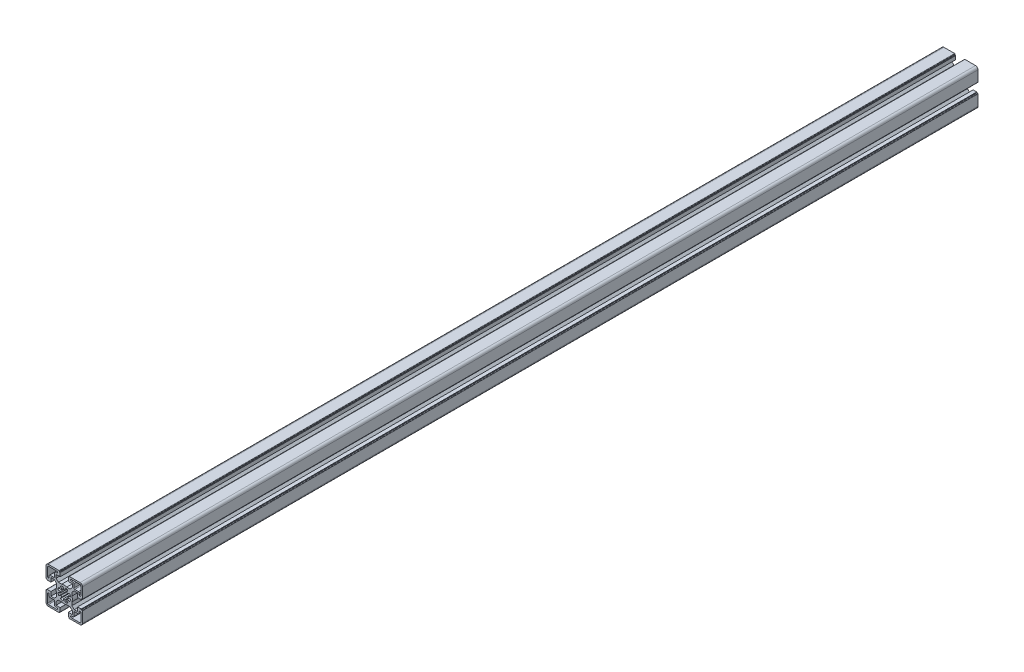
SolidWorks part; units mm, degrees
material "7079 Alloy"
ref_plane "Front Plane" through (0, 0, 0) normal (0, 0, 1) x (1, 0, 0)
ref_plane "Top Plane" through (0, 0, 0) normal (0, 1, 0) x (1, 0, 0)
ref_plane "Right Plane" through (0, 0, 0) normal (1, 0, 0) x (0, 0, -1)
sketch "Sketch1" plane through (0, 0, 0) normal (0, 0, 1) x (1, 0, 0)
  line L0 (0, 34.901) -> (0, -38.8683) construction
  line L1 (-27.7848, 0) -> (42.6814, 0) construction
  line L88 (0.8682, 4.924) -> (1.3892, 7.8784)
  line L89 (-0.8682, 4.924) -> (-1.3892, 7.8785)
  line L90 (-4.5886, 6.5532) -> (-2.8679, 4.0957)
  line L91 (-4.0957, 2.8679) -> (-6.5532, 4.5886)
  line L92 (-7.8784, 1.3892) -> (-4.924, 0.8682)
  line L93 (-7.8785, -1.3892) -> (-4.924, -0.8682)
  line L94 (-6.5532, -4.5886) -> (-4.0957, -2.8679)
  line L95 (-4.5886, -6.5532) -> (-2.8679, -4.0957)
  line L96 (-1.3892, -7.8784) -> (-0.8682, -4.924)
  line L97 (0.8682, -4.924) -> (1.3892, -7.8784)
  line L98 (4.5886, -6.5532) -> (2.8679, -4.0957)
  line L99 (4.0957, -2.8679) -> (6.5532, -4.5886)
  line L100 (7.8784, -1.3892) -> (4.924, -0.8682)
  line L101 (4.924, 0.8682) -> (7.8784, 1.3892)
  line L102 (4.0957, 2.8679) -> (6.5532, 4.5886)
  line L103 (2.8679, 4.0957) -> (4.5886, 6.5532)
  line L104 (-5, -16.4999) -> (-5, -20.9999)
  line L105 (-5, -20.9999) -> (-5.8, -20.9999)
  line L106 (-5.8, -20.9999) -> (-5.8, -22)
  line L107 (-6.3, -22.5) -> (-19.5, -22.5)
  line L108 (-22.5, -19.5) -> (-22.5, -6.2999)
  line L109 (-22, -5.7999) -> (-21, -5.7999)
  line L110 (-21, -5.7999) -> (-21, -4.9999)
  line L111 (-21, -4.9999) -> (-16.5, -4.9999)
  line L112 (-16.5, -4.9999) -> (-16.5, -10.0499)
  line L113 (-16.5, -10.0499) -> (-12.3429, -10.0499)
  line L114 (-12.3429, -10.0499) -> (-9.5, -7.207)
  line L115 (-9.5, -7.207) -> (-9.5, -3.1226)
  line L116 (-9.5, 3.1227) -> (-9.5, 7.207)
  line L117 (-9.5, 7.207) -> (-12.3429, 10.0499)
  line L118 (-12.3429, 10.0499) -> (-16.5, 10.0499)
  line L119 (-16.5, 10.0499) -> (-16.5, 4.9999)
  line L120 (-16.5, 4.9999) -> (-21, 4.9999)
  line L121 (-21, 4.9999) -> (-21, 5.7999)
  line L122 (-21, 5.7999) -> (-22, 5.7999)
  line L123 (-22.5, 6.2999) -> (-22.5, 19.5)
  line L124 (-19.5, 22.5) -> (-6.3, 22.5)
  line L125 (-5.7999, 21.9999) -> (-5.7999, 20.9999)
  line L126 (-5.7999, 20.9999) -> (-5, 20.9999)
  line L127 (-5, 20.9999) -> (-5, 16.5)
  line L128 (-5, 16.5) -> (-10.0501, 16.5)
  line L129 (-10.0501, 16.5) -> (-10.0501, 12.3428)
  line L130 (-10.0501, 12.3428) -> (-7.2072, 9.4999)
  line L131 (-7.2072, 9.4999) -> (-3.1228, 9.4999)
  line L132 (3.1226, 9.4999) -> (7.207, 9.4999)
  line L133 (7.207, 9.4999) -> (10.0499, 12.3428)
  line L134 (10.0499, 12.3428) -> (10.0499, 16.5)
  line L135 (10.0499, 16.5) -> (5, 16.5)
  line L136 (5, 16.5) -> (5, 21)
  line L137 (5, 21) -> (5.7999, 21)
  line L138 (5.7999, 21) -> (5.7999, 21.9999)
  line L139 (6.3, 22.5) -> (19.5001, 22.5)
  line L140 (22.5001, 6.2999) -> (22.5001, 19.5)
  line L141 (22.0001, 5.7999) -> (21, 5.7999)
  line L142 (21, 5.7999) -> (21, 4.9999)
  line L143 (21, 4.9999) -> (16.5, 4.9999)
  line L144 (16.5, 4.9999) -> (16.5, 10.0499)
  line L145 (16.5, 10.0499) -> (12.3429, 10.0499)
  line L146 (12.3429, 10.0499) -> (9.4999, 7.207)
  line L147 (9.4999, 7.207) -> (9.4999, 3.1227)
  line L148 (9.4999, -3.1226) -> (9.4999, -7.207)
  line L149 (9.4999, -7.207) -> (12.3429, -10.0499)
  line L150 (12.3429, -10.0499) -> (16.5, -10.0499)
  line L151 (16.5, -10.0499) -> (16.5, -4.9999)
  line L152 (16.5, -4.9999) -> (21, -4.9999)
  line L153 (21, -4.9999) -> (21, -5.7999)
  line L154 (21, -5.7999) -> (22.0001, -5.7999)
  line L155 (22.5001, -6.2999) -> (22.5001, -19.5)
  line L156 (6.3, -22.5) -> (19.5001, -22.5)
  line L157 (5.8, -22) -> (5.8, -20.9999)
  line L158 (5.8, -20.9999) -> (5, -20.9999)
  line L159 (5, -20.9999) -> (5, -16.4999)
  line L160 (5, -16.4999) -> (10.0499, -16.4999)
  line L161 (10.0499, -16.4999) -> (10.0499, -12.3428)
  line L162 (10.0499, -12.3428) -> (7.2069, -9.4998)
  line L163 (7.2069, -9.4998) -> (3.1226, -9.4998)
  line L164 (-3.1228, -9.4998) -> (-7.2071, -9.4998)
  line L165 (-7.2071, -9.4998) -> (-10.0501, -12.3428)
  line L166 (-10.0501, -12.3428) -> (-10.0501, -16.4999)
  line L167 (-10.0501, -16.4999) -> (-5, -16.4999)
  line L168 (-17.5001, -12) -> (-13.0001, -12)
  line L169 (-12.0001, -17.4999) -> (-12.0001, -13)
  line L170 (-11.0001, -18.4999) -> (-9.0001, -18.4999)
  line L171 (-19.5001, -20.5) -> (-9.0001, -20.5)
  line L172 (-20.5001, -19.5) -> (-20.5001, -8.9999)
  line L173 (-18.5001, -11) -> (-18.5001, -8.9999)
  line L174 (13, -12) -> (17.5, -12)
  line L175 (12, -17.4999) -> (12, -13)
  line L176 (9, -18.4999) -> (11, -18.4999)
  line L177 (9, -20.5) -> (19.5, -20.5)
  line L178 (20.5, -19.5) -> (20.5, -9.0001)
  line L179 (18.5, -11) -> (18.5, -9.0001)
  line L180 (-17.5001, 12) -> (-13.0001, 12)
  line L181 (-12.0001, 13) -> (-12.0001, 17.4999)
  line L182 (-11.0001, 18.4999) -> (-9.0001, 18.4999)
  line L183 (-19.5001, 20.5) -> (-9.0001, 20.5)
  line L184 (-20.5001, 8.9999) -> (-20.5001, 19.5)
  line L185 (-18.5001, 8.9999) -> (-18.5001, 11)
  line L186 (13, 12) -> (17.5, 12)
  line L187 (12, 13) -> (12, 17.4999)
  line L188 (9, 18.4999) -> (11, 18.4999)
  line L189 (9, 20.5) -> (19.5, 20.5)
  line L190 (20.5, 9.0001) -> (20.5, 19.5)
  line L191 (18.5, 9.0001) -> (18.5, 11)
  arc A56 (0.8682, 4.924) -> (-0.8682, 4.924) centre (0, 0) ccw
  arc A57 (-1.3892, 7.8785) -> (-4.5886, 6.5532) centre (0, 0) ccw
  arc A58 (-2.8679, 4.0957) -> (-4.0957, 2.8679) centre (0, 0) ccw
  arc A59 (-6.5532, 4.5886) -> (-7.8784, 1.3892) centre (0, 0) ccw
  arc A60 (-4.924, 0.8682) -> (-4.924, -0.8682) centre (0, 0) ccw
  arc A61 (-7.8785, -1.3892) -> (-6.5532, -4.5886) centre (0, 0) ccw
  arc A62 (-4.0957, -2.8679) -> (-2.8679, -4.0957) centre (0, 0) ccw
  arc A63 (-4.5886, -6.5532) -> (-1.3892, -7.8784) centre (0, 0) ccw
  arc A64 (-0.8682, -4.924) -> (0.8682, -4.924) centre (0, 0) ccw
  arc A65 (1.3892, -7.8784) -> (4.5886, -6.5532) centre (0, 0) ccw
  arc A66 (2.8679, -4.0957) -> (4.0957, -2.8679) centre (0, 0) ccw
  arc A67 (6.5532, -4.5886) -> (7.8784, -1.3892) centre (0, 0) ccw
  arc A68 (4.924, -0.8682) -> (4.924, 0.8682) centre (0, 0) ccw
  arc A69 (7.8784, 1.3892) -> (6.5532, 4.5886) centre (0, 0) ccw
  arc A70 (4.0957, 2.8679) -> (2.8679, 4.0957) centre (0, 0) ccw
  arc A71 (4.5886, 6.5532) -> (1.3892, 7.8784) centre (0, 0) ccw
  arc A72 (-6.3, -22.5) -> (-5.8, -22) centre (-6.3, -22) ccw
  arc A73 (-22.5, -19.5) -> (-19.5, -22.5) centre (-19.5, -19.5) ccw
  arc A74 (-22, -5.7999) -> (-22.5, -6.2999) centre (-22, -6.2999) ccw
  arc A75 (-9.5, 3.1227) -> (-9.5, -3.1226) centre (0, 0.0001) ccw
  arc A76 (-22.5, 6.2999) -> (-22, 5.7999) centre (-22, 6.2999) ccw
  arc A77 (-19.5, 22.5) -> (-22.5, 19.5) centre (-19.5, 19.5) ccw
  arc A78 (-5.7999, 21.9999) -> (-6.3, 22.5) centre (-6.3, 21.9999) ccw
  arc A79 (3.1226, 9.4999) -> (-3.1228, 9.4999) centre (-0.0001, -0.0001) ccw
  arc A80 (6.3, 22.5) -> (5.7999, 21.9999) centre (6.3, 21.9999) ccw
  arc A81 (22.5001, 19.5) -> (19.5001, 22.5) centre (19.5001, 19.5) ccw
  arc A82 (22.0001, 5.7999) -> (22.5001, 6.2999) centre (22.0001, 6.2999) ccw
  arc A83 (9.4999, -3.1226) -> (9.4999, 3.1227) centre (0, 0.0001) ccw
  arc A84 (22.5001, -6.2999) -> (22.0001, -5.7999) centre (22.0001, -6.2999) ccw
  arc A85 (19.5001, -22.5) -> (22.5001, -19.5) centre (19.5001, -19.5) ccw
  arc A86 (5.8, -22) -> (6.3, -22.5) centre (6.3, -22) ccw
  arc A87 (-3.1228, -9.4998) -> (3.1226, -9.4998) centre (-0.0001, 0.0001) ccw
  arc A88 (-18.5001, -11) -> (-17.5001, -12) centre (-17.5001, -11) ccw
  arc A89 (-12.0001, -13) -> (-13.0001, -12) centre (-13.0001, -13) ccw
  arc A90 (-12.0001, -17.4999) -> (-11.0001, -18.4999) centre (-11.0001, -17.4999) ccw
  arc A91 (-9.0001, -20.5) -> (-9.0001, -18.4999) centre (-9.0001, -19.5) ccw
  arc A92 (-20.5001, -19.5) -> (-19.5001, -20.5) centre (-19.5001, -19.5) ccw
  arc A93 (-18.5001, -8.9999) -> (-20.5001, -8.9999) centre (-19.5001, -8.9999) ccw
  arc A94 (17.5, -12) -> (18.5, -11) centre (17.5, -11) ccw
  arc A95 (13, -12) -> (12, -13) centre (13, -13) ccw
  arc A96 (11, -18.4999) -> (12, -17.4999) centre (11, -17.4999) ccw
  arc A97 (9, -18.4999) -> (9, -20.5) centre (9, -19.5) ccw
  arc A98 (19.5, -20.5) -> (20.5, -19.5) centre (19.5, -19.5) ccw
  arc A99 (20.5, -9.0001) -> (18.5, -9.0001) centre (19.5, -9.0001) ccw
  arc A100 (-17.5001, 12) -> (-18.5001, 11) centre (-17.5001, 11) ccw
  arc A101 (-13.0001, 12) -> (-12.0001, 13) centre (-13.0001, 13) ccw
  arc A102 (-11.0001, 18.4999) -> (-12.0001, 17.4999) centre (-11.0001, 17.4999) ccw
  arc A103 (-9.0001, 18.4999) -> (-9.0001, 20.5) centre (-9.0001, 19.5) ccw
  arc A104 (-19.5001, 20.5) -> (-20.5001, 19.5) centre (-19.5001, 19.5) ccw
  arc A105 (-20.5001, 8.9999) -> (-18.5001, 8.9999) centre (-19.5001, 8.9999) ccw
  arc A106 (18.5, 11) -> (17.5, 12) centre (17.5, 11) ccw
  arc A107 (12, 13) -> (13, 12) centre (13, 13) ccw
  arc A108 (12, 17.4999) -> (11, 18.4999) centre (11, 17.4999) ccw
  arc A109 (9, 20.5) -> (9, 18.4999) centre (9, 19.5) ccw
  arc A110 (20.5, 19.5) -> (19.5, 20.5) centre (19.5, 19.5) ccw
  arc A111 (18.5, 9.0001) -> (20.5, 9.0001) centre (19.5, 9.0001) ccw
  dimension "D5" = 10
  dimension "D1" = 45.0001
  dimension "D2" = 44.9999
  dimension "D3" = 12.5001
  dimension "D4" = 10
  dimension "D6" = 22.5001
extrude "Base-Extrude" add sketch "Sketch1" along normal blind 1106
